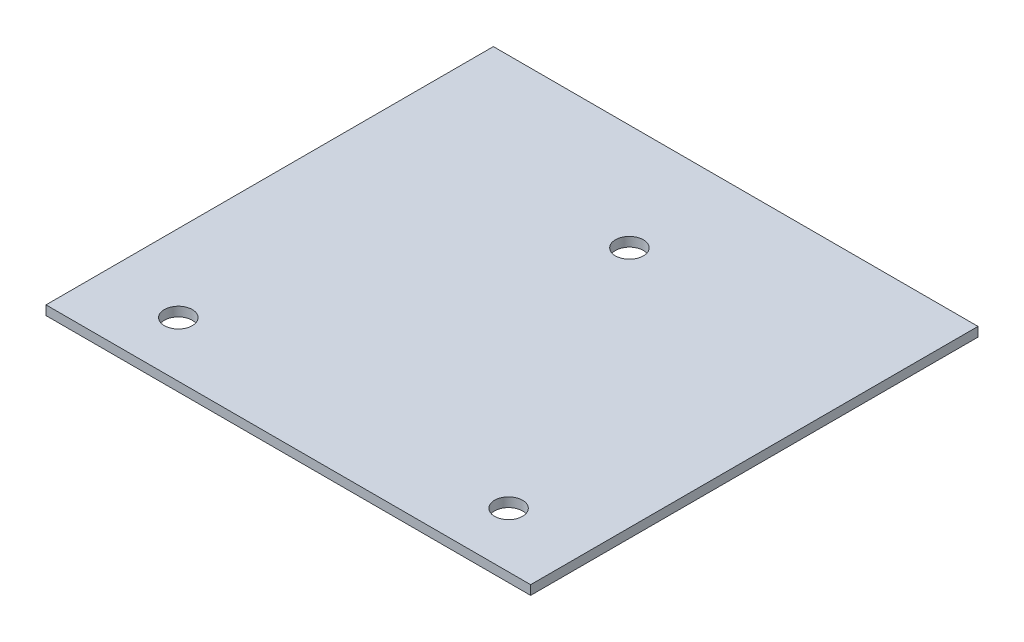
SolidWorks part; units mm, degrees
material "Cedar"
ref_plane "Front Plane" through (0, 0, 0) normal (0, 0, 1) x (1, 0, 0)
ref_plane "Top Plane" through (0, 0, 0) normal (0, 1, 0) x (1, 0, 0)
ref_plane "Right Plane" through (0, 0, 0) normal (1, 0, 0) x (0, 0, -1)
sketch "Sketch1" plane through (0, 0, 0) normal (0, 1, 0) x (1, 0, 0)
  line L1 (0, 0) -> (660.4, 0)
  line L2 (0, 0) -> (0, 609.6)
  line L3 (0, 609.6) -> (660.4, 609.6)
  line L4 (660.4, 0) -> (660.4, 609.6)
  dimension "D1" = 660.4
  dimension "D2" = 609.6
extrude "Boss-Extrude1" add sketch "Sketch1" along normal blind 12.7
sketch "Sketch5" plane through (0, 12.7, 0) normal (0, 1, 0) x (1, 0, 0)
  line L0 (330.2, 609.6) -> (330.2, 464.8281) construction
  line L1 (660.4, 609.6) -> (0, 609.6) construction
  line L2 (0, 0) -> (105.2, 75.1166) construction
  line L3 (660.4, 0) -> (555.2, 75.1166) construction
  line L5 (330.2, 464.8281) -> (105.2, 75.1166) construction
  line L6 (105.2, 75.1166) -> (555.2, 75.1166) construction
  line L7 (555.2, 75.1166) -> (330.2, 464.8281) construction
  line L8 (330.2, 464.8281) -> (330.2, 75.1166) construction
  circle A0 centre (105.2, 75.1166) radius 19.05
  circle A1 centre (555.2, 75.1166) radius 19.05
  circle A2 centre (330.2, 464.8281) radius 19.05
  dimension "D6" = 38.1
  dimension "D7" = 38.1
  dimension "D8" = 38.1
  dimension "D1" = 450
extrude "Cut-Extrude2" cut sketch "Sketch5" against normal through all
sketch "Sketch6" plane through (0, 12.7, 0) normal (0, 1, 0) x (1, 0, 0)
  line L0 (0, 609.6) -> (660.4, 0) construction
  line L1 (660.4, 609.6) -> (0, 0) construction
  point P8 (330.2, 304.8)
sketch "Sketch7" plane through (0, 12.7, 0) normal (0, 1, 0) x (1, 0, 0)
  circle A0 centre (17.9605, 17.9605) radius 17
